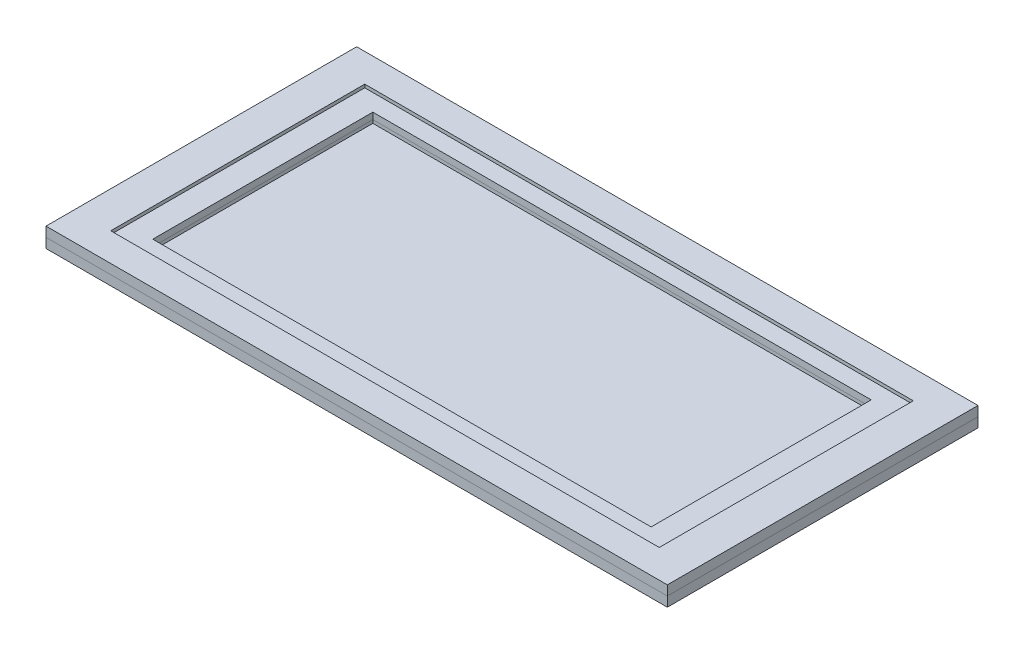
SolidWorks part; units mm, degrees
ref_plane "Front Plane" through (0, 0, 0) normal (0, 0, 1) x (1, 0, 0)
ref_plane "Top Plane" through (0, 0, 0) normal (0, 1, 0) x (1, 0, 0)
ref_plane "Right Plane" through (0, 0, 0) normal (1, 0, 0) x (0, 0, -1)
sketch "Sketch1" plane through (0, 0, 0) normal (0, 1, 0) x (1, 0, 0)
  line L1 (-609.6, -304.8) -> (609.6, -304.8)
  line L2 (-609.6, -304.8) -> (-609.6, 304.8)
  line L3 (-609.6, 304.8) -> (609.6, 304.8)
  line L4 (609.6, -304.8) -> (609.6, 304.8)
  line L5 (-609.6, -304.8) -> (609.6, 304.8) construction
  line L6 (-609.6, 304.8) -> (609.6, -304.8) construction
  point P0 (0, 0)
  dimension "D1" = 1219.2
  dimension "D2" = 609.6
extrude "MDF_Slab1" add sketch "Sketch1" along normal blind 19.05
sketch "Sketch2" plane through (0, 19.05, 0) normal (0, 1, 0) x (1, 0, 0)
  line L1 (609.6, -304.8) -> (-609.6, -304.8)
  line L2 (609.6, -304.8) -> (609.6, 304.8)
  line L3 (609.6, 304.8) -> (-609.6, 304.8)
  line L4 (-609.6, -304.8) -> (-609.6, 304.8)
  line L5 (609.6, -304.8) -> (-609.6, 304.8) construction
  line L6 (609.6, 304.8) -> (-609.6, -304.8) construction
  point P0 (0, 0)
extrude "MDF_Slab2" add sketch "Sketch2" along normal blind 19.05 separate body
sketch "Sketch3" plane through (0, 38.1, 0) normal (0, 1, 0) x (1, 0, 0)
  line L1 (538.1625, -249.2375) -> (-538.1625, -249.2375)
  line L2 (538.1625, -249.2375) -> (538.1625, 249.2375)
  line L3 (538.1625, 249.2375) -> (-538.1625, 249.2375)
  line L4 (-538.1625, -249.2375) -> (-538.1625, 249.2375)
  line L5 (538.1625, -249.2375) -> (-538.1625, 249.2375) construction
  line L6 (538.1625, 249.2375) -> (-538.1625, -249.2375) construction
  point P0 (0, 0)
  dimension "D1" = 1076.325
  dimension "D2" = 498.475
extrude "Window_Cut" cut sketch "Sketch3" against normal blind 6.35
sketch "Sketch4" plane through (0, 31.75, 0) normal (0, 1, 0) x (1, 0, 0)
  line L1 (488.95, -215.9) -> (-488.95, -215.9)
  line L2 (488.95, -215.9) -> (488.95, 215.9)
  line L3 (488.95, 215.9) -> (-488.95, 215.9)
  line L4 (-488.95, -215.9) -> (-488.95, 215.9)
  line L5 (488.95, -215.9) -> (-488.95, 215.9) construction
  line L6 (488.95, 215.9) -> (-488.95, -215.9) construction
  point P0 (0, 0)
  dimension "D1" = 431.8
  dimension "D2" = 977.9
extrude "Mirror_Cut" cut sketch "Sketch4" against normal blind 19.05
